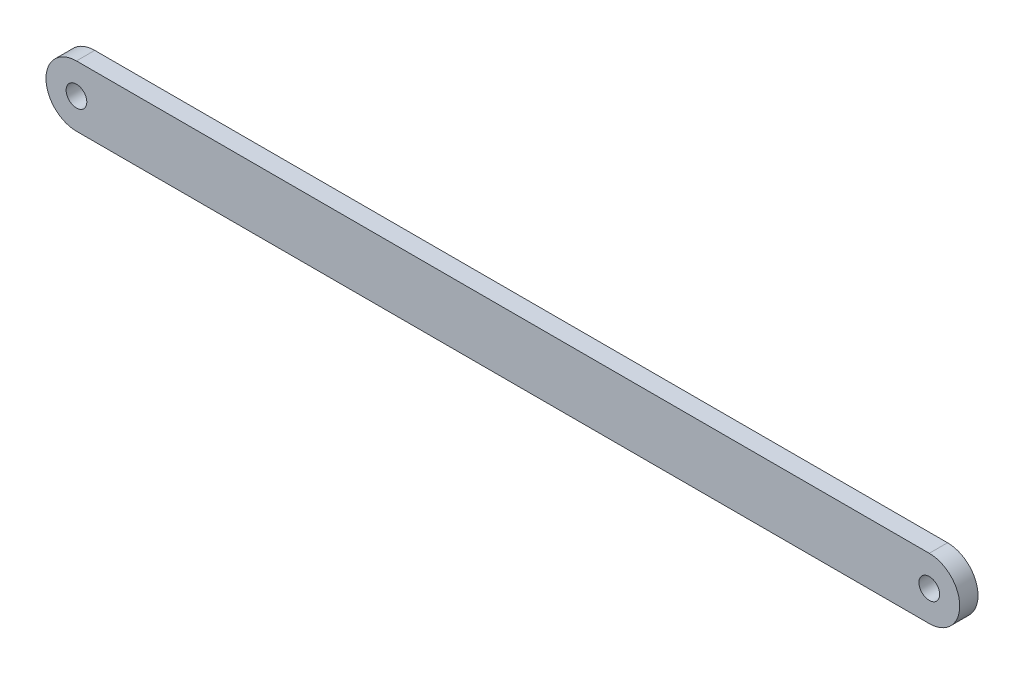
SolidWorks part; units mm, degrees
material "1023 Kohlenstoffstahlblech (SS)"
ref_plane "Ebene vorne" through (0, 0, 0) normal (0, 0, 1) x (1, 0, 0)
ref_plane "Ebene oben" through (0, 0, 0) normal (0, 1, 0) x (1, 0, 0)
ref_plane "Ebene rechts" through (0, 0, 0) normal (1, 0, 0) x (0, 0, -1)
sketch "Skizze1" plane through (0, 0, 0) normal (0, 0, 1) x (1, 0, 0)
  line L0 (-70, 0) -> (70, 0) construction
  line L1 (-70, 5) -> (70, 5)
  line L2 (-70, -5) -> (70, -5)
  arc A0 (-70, 5) -> (-70, -5) centre (-70, 0) ccw
  arc A1 (70, -5) -> (70, 5) centre (70, 0) ccw
  point P2 (0, 0)
  dimension "D1" = 140
  dimension "D2" = 10
extrude "Aufsatz-Linear austragen1" add sketch "Skizze1" along normal mid plane 3
hole_wizard "Durchgangsloch für M31" positions "Skizze2" profile "Skizze3" hole size "M3" standard "ANSI Metrisch" end condition through all
sketch "Skizze2" plane through (0, 0, 1.5) normal (0, 0, 1) x (1, 0, 0)
  arc A0 (-70, 5) -> (-70, -5) centre (-70, 0) ccw construction
  arc A1 (-70, 5) -> (-70, -5) centre (-70, 0) ccw construction
  arc A2 (70, -5) -> (70, 5) centre (70, 0) ccw construction
  arc A3 (70, -5) -> (70, 5) centre (70, 0) ccw construction
  point P1 (-70, 0)
  point P4 (70, 0)
sketch "Skizze3" plane through (-70, 0, 1.5) normal (1, 0, 0) x (0, -1, 0)
  line L0 (0, 0) -> (0, 3)
  line L1 (0, 3) -> (1.7, 3)
  line L2 (1.7, 3) -> (1.7, 0)
  line L5 (1.7, 0) -> (0, 0)
  line L11 (0, -6.35) -> (0, 107.95) construction
  dimension "Bohrerdurchmesser" = 3.4
  dimension "Bohrungstiefe" = 3
sketch "Skizze4" [suppressed] plane through (0, 0, 1) normal (0, 0, 1) x (1, 0, 0)
  line L0 (40, 5) -> (190, 5)
  line L1 (190, 5) -> (190, -5)
  line L2 (190, -5) -> (40, -5)
  arc A0 (40, -5) -> (40, 5) centre (40, 0) ccw construction
  arc A1 (40, -5) -> (40, 5) centre (40, 0) ccw
  dimension "D1" = 150
extrude "Aufsatz-Linear austragen2" [suppressed] add sketch "Skizze4" against normal up to surface (2 mm away)
